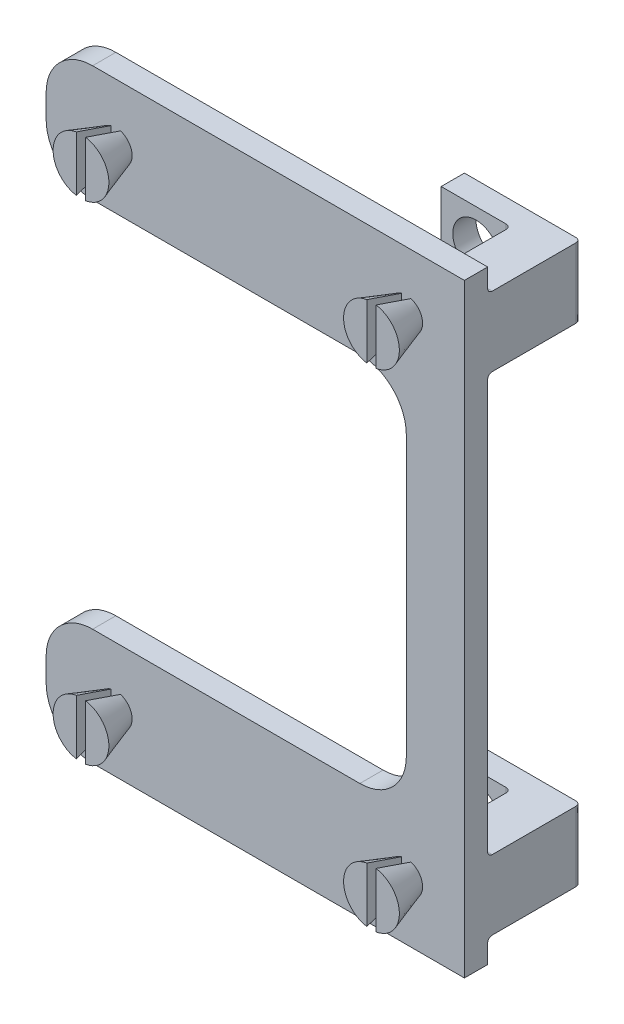
SolidWorks part; units mm, degrees
ref_plane "Ön Düzlem" through (0, 0, 0) normal (0, 0, 1) x (1, 0, 0)
ref_plane "Üst Düzlem" through (0, 0, 0) normal (0, 1, 0) x (1, 0, 0)
ref_plane "Sağ Düzlem" through (0, 0, 0) normal (1, 0, 0) x (0, 0, -1)
sketch "Çizim1" plane through (0, 0, 0) normal (0, 0, 1) x (1, 0, 0)
  line L0 (-12, 0) -> (12, 0) construction
  line L1 (-0.0167, -12.5) -> (-0.0167, 12.5) construction
  line L2 (-12.5, -13) -> (12.5, -13)
  line L3 (-12.5, -13) -> (-12.5, 13)
  line L4 (-12.5, 13) -> (12.5, 13)
  line L5 (12.5, -13) -> (12.5, 13)
  line L6 (-12.5, -13) -> (12.5, 13) construction
  line L7 (-12.5, 13) -> (12.5, -13) construction
  dimension "D1" = 26
extrude "Yükseklik-Ekstrüzyon1" add sketch "Çizim1" along normal blind 1
sketch "Çizim2" plane through (0, 0, 1) normal (0, 0, 1) x (1, 0, 0)
  line L8 (10, 0) -> (12.5, 0) construction
  line L9 (-2.5, 10.5) -> (10, 10.5) construction
  line L10 (-2.5, 10.5) -> (-2.5, -10.5) construction
  line L11 (-2.5, -10.5) -> (10, -10.5) construction
  line L12 (10, 10.5) -> (10, -10.5) construction
  circle A0 centre (10, 10.5) radius 1
  circle A1 centre (-2.5, 10.5) radius 1
  circle A2 centre (10, -10.5) radius 1
  circle A3 centre (-2.5, -10.5) radius 1
  point P0 (0, 0)
ref_plane "Düzlem2" through (0, 10.5, 0) normal (0, 1, 0) x (1, 0, 0)
sketch "Çizim9" plane through (0, 10.5, 0) normal (0, 1, 0) x (1, 0, 0)
  line L0 (-2.5, -1) -> (-2.5, -2.5)
  line L1 (-3.5, -1) -> (-1.5, -1) construction
  line L2 (-2.5, -2.5) -> (-3.7, -2.5)
  line L4 (-2.5, -1) -> (-3.2, -1)
  line L5 (-3.7, -2.5) -> (-3.2, -1)
  dimension "D1" = 1.5
  dimension "D2" = 0.7
  dimension "D3" = 1.2
revolve "Döndür1" add sketch "Çizim9" angle 360 about L0
sketch "Çizim11" plane through (0, 10.5, 0) normal (0, 1, 0) x (1, 0, 0)
  line L0 (10, -1) -> (10, -2.5)
  line L1 (10, -2.5) -> (8.8, -2.5)
  line L2 (10, -1) -> (9.3, -1)
  line L3 (8.8, -2.5) -> (9.3, -1)
  dimension "D1" = 1.5
  dimension "D2" = 0.7
  dimension "D3" = 1.2
revolve "Döndür2" add sketch "Çizim11" angle 360 about L0
mirror "Aynalama1" about plane through (0, 0, 0) normal (0, 1, 0) of "Döndür2", "Döndür1"
sketch "Çizim12" plane through (0, 10.5, 0) normal (0, 1, 0) x (1, 0, 0)
  line L0 (-2.5, -2.5) -> (-2.5, -1) construction
  line L1 (-3.7, -2.5) -> (-1.3, -2.5) construction
  line L2 (-3.5, -1) -> (-1.5, -1) construction
  line L3 (-2.3, -2.5) -> (-2.3, -1)
  line L4 (-2.7, -2.5) -> (-2.7, -1)
  line L5 (-2.7, -1) -> (-2.3, -1)
  line L6 (-2.7, -2.5) -> (-2.3, -2.5)
  line L7 (10, -2.5) -> (10, -1) construction
  line L8 (9.8, -2.5) -> (9.8, -1)
  line L9 (10.2, -2.5) -> (10.2, -1)
  line L10 (9.8, -1) -> (10.2, -1)
  line L11 (9.8, -2.5) -> (10.2, -2.5)
  dimension "D1" = 0.2
  dimension "D2" = 0.2
extrude "Kes-Ekstrüzyon2" cut sketch "Çizim12" against normal blind 25.3 and the other way blind 12
sketch "Çizim13" plane through (0, 0, 0) normal (0, 0, 1) x (1, 0, 0)
  line L1 (-10, -8) -> (10, -8)
  line L2 (-10, -8) -> (-10, 8)
  line L3 (-10, 8) -> (10, 8)
  line L4 (10, -8) -> (10, 8)
  line L5 (-10, -8) -> (10, 8) construction
  line L6 (-10, 8) -> (10, -8) construction
  point P0 (0, 0)
  dimension "D1" = 20
  dimension "D2" = 16
extrude "Kes-Ekstrüzyon4" cut sketch "Çizim13" against normal blind 4 and the other way blind 5 contours L2 L1 L4 L3
fillet "Radyus1" radius 2 4 edges at (-10, -8, 0.5) (10, -8, 0.5) (10, 8, 0.5) (-10, 8, 0.5)
sketch "Çizim14" plane through (0, 0, 0) normal (0, 0, 1) x (1, 0, 0)
  line L0 (-12.5, -13) -> (12.5, -13) construction
  line L1 (-12.5, 13) -> (-5.5, 13)
  line L2 (-12.5, 13) -> (-12.5, -13)
  line L3 (-12.5, -13) -> (-5.5, -13)
  line L4 (-5.5, 13) -> (-5.5, -13)
  dimension "D1" = 7
extrude "Kes-Ekstrüzyon5" cut sketch "Çizim14" against normal blind 3 and the other way blind 3
fillet "Radyus2" radius 2 4 edges at (-5.5, -13, 0.5) (-5.5, -8, 0.5) (-5.5, 8, 0.5) (-5.5, 13, 0.5)
ref_plane "Düzlem3" through (10.5, 0, 0) normal (1, 0, 0) x (0, 0, -1)
sketch "Çizim17" plane through (10.5, 0, 0) normal (1, 0, 0) x (0, 0, -1)
  line L0 (0, 12) -> (4, 12)
  line L1 (0, 12) -> (0, 9)
  line L2 (0, 9) -> (4, 9)
  line L3 (4, 12) -> (4, 9)
  line L4 (-1, 13) -> (0, 13) construction
  dimension "D1" = 3
  dimension "D2" = 4
  dimension "D3" = 1
extrude "Yükseklik-Ekstrüzyon2" add sketch "Çizim17" along normal blind 2
sketch "Çizim18" plane through (0, 0, -4) normal (0, 0, -1) x (-1, 0, 0)
  line L0 (-12.5, 12) -> (-10.5, 12) construction
  line L1 (-11.5, 12) -> (-7.5, 12)
  line L2 (-11.5, 12) -> (-11.5, 9)
  line L3 (-11.5, 9) -> (-7.5, 9)
  line L4 (-7.5, 12) -> (-7.5, 9)
  line L5 (-12.5, 9) -> (-12.5, 12) construction
  dimension "D1" = 3
  dimension "D2" = 1
  dimension "D3" = 4
extrude "Yükseklik-Ekstrüzyon3" add sketch "Çizim18" against normal blind 1
sketch "Çizim19" plane through (0, 0, -4) normal (0, 0, -1) x (-1, 0, 0)
  circle A0 centre (-9, 10.5) radius 1
  dimension "D1" = 2
extrude "Kes-Ekstrüzyon6" cut sketch "Çizim19" against normal blind 1
fillet "Radyus3" radius 0.2 5 edges at (12.5, 10.5, -4) (10.5, 10.5, -3) (11.5, 9, 0) (11.5, 12, 0) (10.5, 10.5, 0)
mirror "Aynalama2" about plane through (0, 0, 0) normal (0, 1, 0) of "Radyus3", "Kes-Ekstrüzyon6", "Yükseklik-Ekstrüzyon3", "Yükseklik-Ekstrüzyon2"
